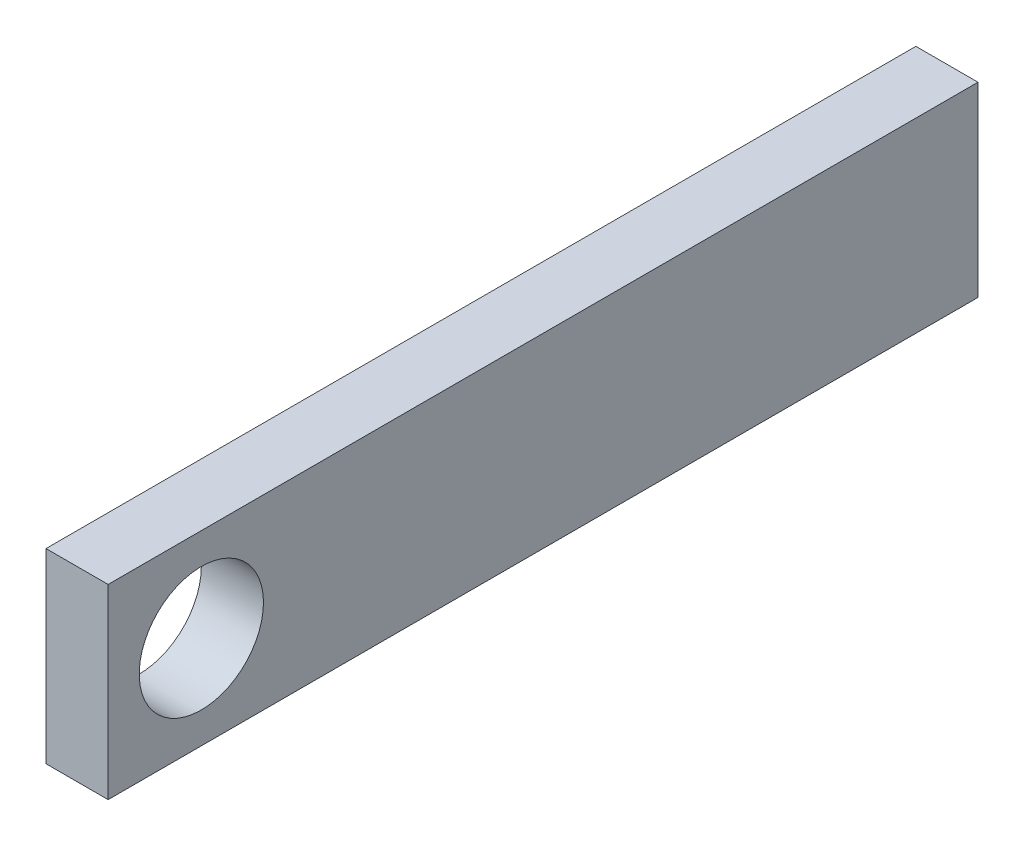
SolidWorks part; units mm, degrees
material "2014-T6"
ref_plane "Front" through (0, 0, 0) normal (0, 0, 1) x (1, 0, 0)
ref_plane "Top" through (0, 0, 0) normal (0, 1, 0) x (1, 0, 0)
ref_plane "Right" through (0, 0, 0) normal (1, 0, 0) x (0, 0, -1)
sketch "Sketch1" plane through (0, 0, 0) normal (1, 0, 0) x (0, 0, -1)
  line L1 (-15, -15) -> (125, -15)
  line L2 (-15, -15) -> (-15, 15)
  line L3 (-15, 15) -> (125, 15)
  line L4 (125, -15) -> (125, 15)
  circle A0 centre (0, 0) radius 10
  dimension "D5" = 20
  dimension "D1" = 15
  dimension "D2" = 140
  dimension "D3" = 30
  dimension "D4" = 15
extrude "Boss-Extrude1" add sketch "Sketch1" along normal blind 10
